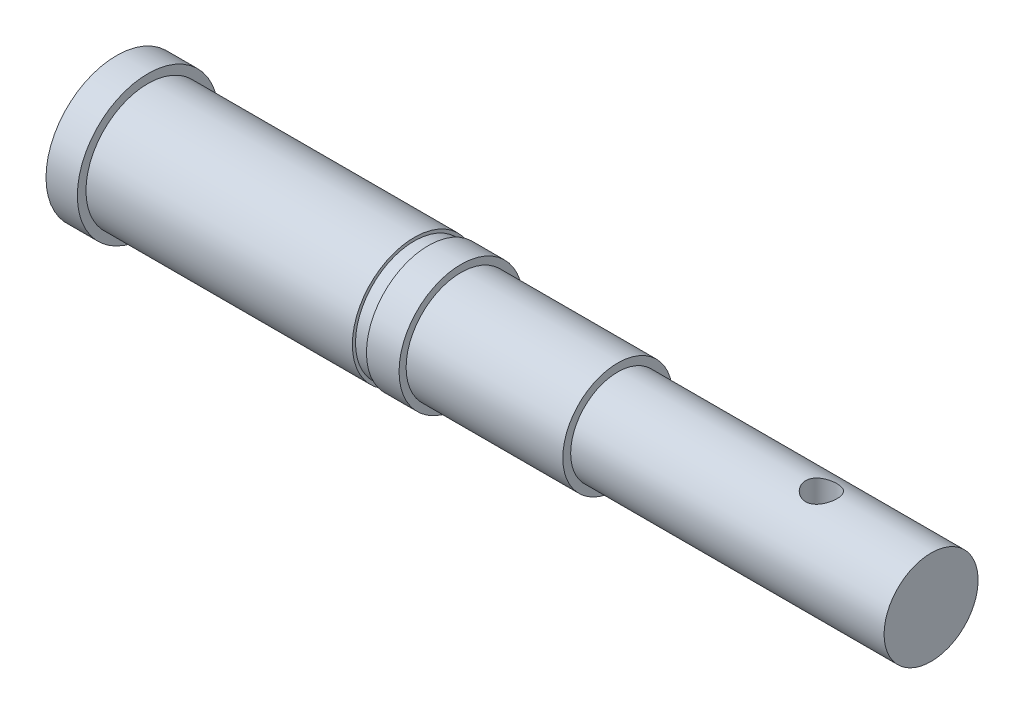
SolidWorks part; units mm, degrees
material "6061 合金"
ref_plane "前视基准面" through (0, 0, 0) normal (0, 0, 1) x (1, 0, 0)
ref_plane "上视基准面" through (0, 0, 0) normal (0, 1, 0) x (1, 0, 0)
ref_plane "右视基准面" through (0, 0, 0) normal (1, 0, 0) x (0, 0, -1)
sketch "草图1" plane through (0, 0, 0) normal (0, 0, 1) x (1, 0, 0)
  line L0 (-33.4091, 0) -> (18.5709, 0)
  line L1 (18.5709, 0) -> (18.5709, 3)
  line L2 (18.5709, 3) -> (-1.4291, 3)
  line L3 (-1.4291, 3) -> (-1.4291, 3.5)
  line L4 (-11.4291, 3.95) -> (-13.5091, 3.95)
  line L5 (-31.4091, 3.95) -> (-31.4091, 4.5)
  line L6 (-31.4091, 4.5) -> (-33.4091, 4.5)
  line L7 (-33.4091, 4.5) -> (-33.4091, 0)
  line L8 (-66.1364, 0) -> (53.6364, 0) construction
  line L9 (-14.4091, 3.95) -> (-14.4091, 3.75)
  line L10 (-13.5091, 3.95) -> (-13.5091, 3.75)
  line L11 (-14.4091, 3.75) -> (-13.5091, 3.75)
  line L12 (-14.4091, 3.95) -> (-31.4091, 3.95)
  line L13 (-11.4291, 3.95) -> (-11.4291, 3.5)
  line L14 (-11.4291, 3.5) -> (-1.4291, 3.5)
  dimension "D1" = 20
  dimension "D2" = 3.5
  dimension "D3" = 17
  dimension "D4" = 0.9
  dimension "D5" = 0.2
  dimension "D6" = 3.95
  dimension "D7" = 3
  dimension "D8" = 4.5
  dimension "D9" = 2
  dimension "D10" = 10
  dimension "D11" = 19.98
revolve "旋转1" add sketch "草图1" angle 360 about L8
sketch "草图2" plane through (0, 0, 0) normal (0, 1, 0) x (1, 0, 0)
  line L0 (33.7089, 0) -> (-9.1342, 0) construction
  line L1 (-1.4291, -3) -> (-1.4291, 3) construction
  circle A0 centre (11.5709, 0) radius 1
  dimension "D1" = 2
  dimension "D2" = 13
extrude "切除-拉伸1" cut sketch "草图2" against normal mid plane 10
